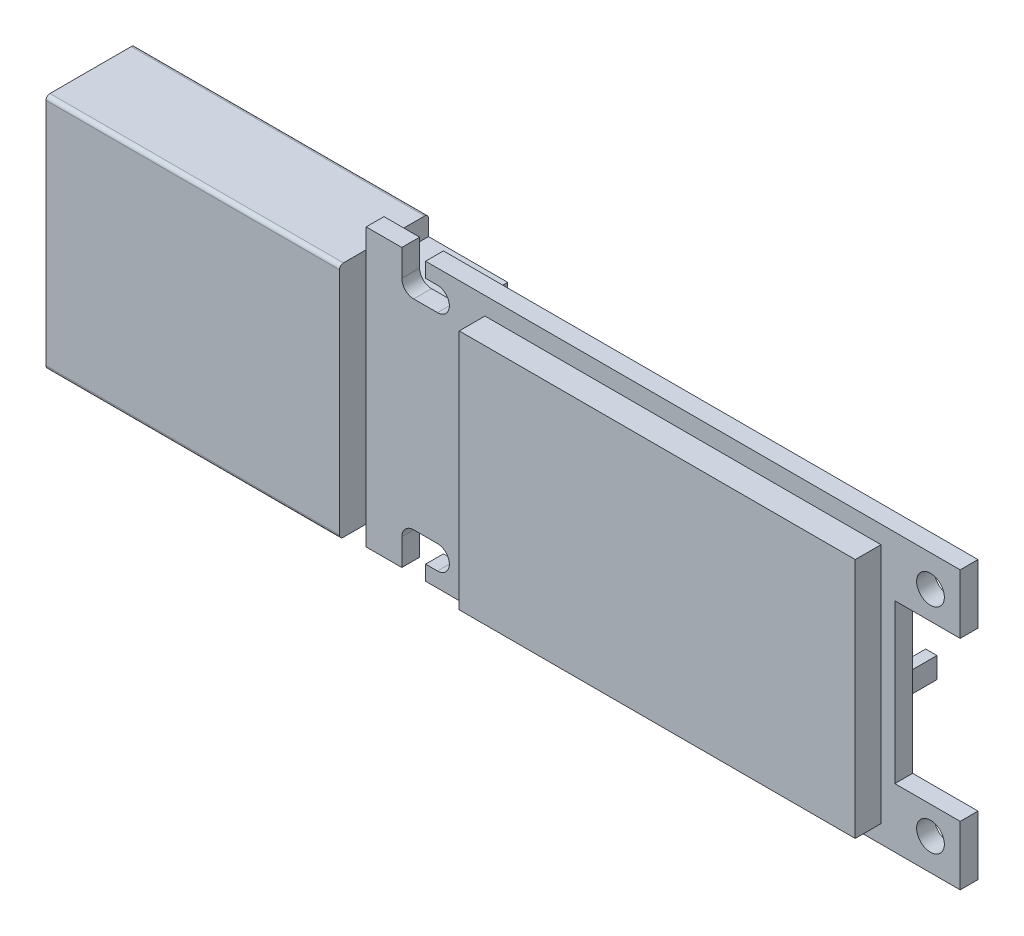
SolidWorks part; units mm, degrees
ref_plane "Plan de face" through (0, 0, 0) normal (0, 0, 1) x (1, 0, 0)
ref_plane "Plan de dessus" through (0, 0, 0) normal (0, 1, 0) x (1, 0, 0)
ref_plane "Plan de droite" through (0, 0, 0) normal (1, 0, 0) x (0, 0, -1)
sketch "Esquisse1" plane through (0, 0, 0) normal (0, 0, 1) x (1, 0, 0)
  line L1 (-7.41, 6) -> (7.41, 6)
  line L2 (-7.41, 6) -> (-7.41, -6)
  line L3 (-7.41, -6) -> (7.41, -6)
  line L4 (7.41, 6) -> (7.41, -6)
  line L5 (-7.41, 6) -> (7.41, -6) construction
  line L6 (-7.41, -6) -> (7.41, 6) construction
  point P0 (0, 0)
  dimension "D1" = 14.82
  dimension "D2" = 12
extrude "Boss.-Extru.1" add sketch "Esquisse1" along normal blind 4.5
sketch "Esquisse2" plane through (-7.41, 0, 0) normal (-1, 0, 0) x (0, 0, 1)
  line L0 (4.5, 6) -> (0, 6) construction
  line L1 (0.3, 5.7) -> (2.3, 5.7)
  line L2 (0.3, 5.7) -> (0.3, -5.7)
  line L3 (0.3, -5.7) -> (2.3, -5.7)
  line L4 (2.3, 5.7) -> (2.3, -5.7)
  line L5 (0, 6) -> (0, -6) construction
  line L6 (4.5, -6) -> (0, -6) construction
  dimension "D1" = 2
  dimension "D2" = 0.3
  dimension "D3" = 0.3
  dimension "D4" = 0.3
extrude "Enlèv. mat.-Extru.1" cut sketch "Esquisse2" against normal blind 9
fillet "Congé1" radius 0.2 4 edges at (0, -6, 0) (0, -6, 4.5) (0, 6, 0) (0, 6, 4.5)
ref_plane "Plan1" through (0, 0, 2.25) normal (0, 0, 1) x (1, 0, 0)
sketch "Esquisse3" plane through (0, 0, 2.25) normal (0, 0, 1) x (1, 0, 0)
  line L0 (0, 0) -> (36.7919, 0) construction
  line L1 (7.41, 7) -> (37.41, 7)
  line L2 (7.41, 7) -> (7.41, -7)
  line L3 (7.41, -7) -> (37.41, -7)
  line L4 (37.41, 7) -> (37.41, -7)
  line L5 (7.41, -5.8) -> (7.41, 5.8) construction
  point P7 (37.41, 0)
  dimension "D1" = 14
  dimension "D2" = 30
extrude "Boss.-Extru.2" add sketch "Esquisse3" along normal blind 0.9
sketch "Esquisse4" plane through (0, 0, 0) normal (0, 0, -1) x (-1, 0, 0)
  line L0 (7.41, 0) -> (-7.41, 0) construction
  line L1 (7.41, 5.8) -> (7.41, -5.8) construction
  line L2 (-7.41, 6) -> (-7.41, -6) construction
  line L3 (-7.41, 6) -> (7.41, 6) construction
  line L4 (0.41, 4.2) -> (2.41, 4.2)
  line L5 (0.41, 4.2) -> (0.41, 1.7)
  line L6 (0.41, 1.7) -> (2.41, 1.7)
  line L7 (2.41, 4.2) -> (2.41, 1.7)
  line L8 (2.41, -4.2) -> (2.41, -1.7)
  line L9 (0.41, -1.7) -> (2.41, -1.7)
  line L10 (0.41, -4.2) -> (0.41, -1.7)
  line L11 (0.41, -4.2) -> (2.41, -4.2)
  dimension "D1" = 2
  dimension "D2" = 2.5
  dimension "D3" = 1.8
  dimension "D4" = 5
extrude "Enlèv. mat.-Extru.2" cut sketch "Esquisse4" against normal up to next
sketch "Esquisse5" plane through (0, 0, 3.15) normal (0, 0, 1) x (1, 0, 0)
  line L0 (37.41, 0) -> (7.41, 0) construction
  line L1 (37.41, -7) -> (37.41, 7) construction
  line L2 (7.41, 6) -> (7.41, -6) construction
  line L3 (35.91, 7) -> (35.91, -7) construction
  line L4 (37.41, 4) -> (34.11, 4)
  line L5 (37.41, 4) -> (37.41, -4)
  line L6 (37.41, -4) -> (34.11, -4)
  line L7 (34.11, 4) -> (34.11, -4)
  line L8 (37.41, 7) -> (7.41, 7) construction
  line L9 (7.41, -7) -> (37.41, -7) construction
  line L10 (7.41, 7) -> (7.41, 6) construction
  line L11 (9.81, 5.65) -> (11.01, 5.65) construction
  line L12 (9.81, 6.25) -> (11.01, 6.25)
  line L13 (9.81, 5.05) -> (11.01, 5.05)
  line L14 (7.41, -5.8) -> (7.41, 5.8) construction
  line L15 (9.81, -5.65) -> (11.01, -5.65) construction
  line L16 (9.81, -6.25) -> (11.01, -6.25)
  line L17 (9.81, -5.05) -> (11.01, -5.05)
  circle A0 centre (35.91, 5.4) radius 0.7
  circle A1 centre (35.91, -5.4) radius 0.7
  arc A2 (9.81, 6.25) -> (9.81, 5.05) centre (9.81, 5.65) ccw
  arc A3 (11.01, 5.05) -> (11.01, 6.25) centre (11.01, 5.65) ccw
  arc A4 (9.81, -6.25) -> (9.81, -5.05) centre (9.81, -5.65) cw
  arc A5 (11.01, -5.05) -> (11.01, -6.25) centre (11.01, -5.65) cw
  point P10 (34.11, 0)
  point P25 (10.41, 5.65)
  point P34 (10.41, -5.65)
  dimension "D4" = 1.4
  dimension "D1" = 8
  dimension "D2" = 3.3
  dimension "D3" = 28.5
  dimension "D5" = 10.8
  dimension "D6" = 3
  dimension "D7" = 1.2
  dimension "D8" = 1.2
  dimension "D9" = 11.3
extrude "Enlèv. mat.-Extru.3" cut sketch "Esquisse5" against normal through all
sketch "Esquisse6" plane through (0, 0, 3.15) normal (0, 0, 1) x (1, 0, 0)
  line L0 (-7.41, 0) -> (34.11, 0) construction
  line L1 (13.41, 6.1) -> (33.41, 6.1)
  line L2 (13.41, 6.1) -> (13.41, -6.1)
  line L3 (13.41, -6.1) -> (33.41, -6.1)
  line L4 (33.41, 6.1) -> (33.41, -6.1)
  line L5 (-7.41, 5.8) -> (-7.41, -5.8) construction
  line L6 (34.11, 4) -> (34.11, -4) construction
  line L7 (7.41, 6) -> (7.41, -6) construction
  point P10 (13.41, 0)
  dimension "D1" = 12.2
  dimension "D2" = 20
  dimension "D3" = 26
extrude "Boss.-Extru.3" add sketch "Esquisse6" along normal blind 1.3
sketch "Esquisse7" plane through (0, 0, 2.25) normal (0, 0, -1) x (-1, 0, 0)
  line L1 (-30.8694, 3.363) -> (-22.672, 3.363)
  line L2 (-30.8694, 3.363) -> (-30.8694, -3.4681)
  line L3 (-30.8694, -3.4681) -> (-22.672, -3.4681)
  line L4 (-22.672, 3.363) -> (-22.672, -3.4681)
  line L5 (-18.4681, -2.207) -> (-17.1019, -2.207)
  line L6 (-18.4681, -2.207) -> (-18.4681, -4.3089)
  line L7 (-18.4681, -4.3089) -> (-17.1019, -4.3089)
  line L8 (-17.1019, -2.207) -> (-17.1019, -4.3089)
  line L9 (-15.3153, -2.207) -> (-14.0541, -2.207)
  line L10 (-15.3153, -2.207) -> (-15.3153, -4.3089)
  line L11 (-15.3153, -4.3089) -> (-14.0541, -4.3089)
  line L12 (-14.0541, -2.207) -> (-14.0541, -4.3089)
  line L13 (-19.6242, 3.363) -> (-17.1019, 3.363)
  line L14 (-19.6242, 3.363) -> (-19.6242, 2.3121)
  line L15 (-19.6242, 2.3121) -> (-17.1019, 2.3121)
  line L16 (-17.1019, 3.363) -> (-17.1019, 2.3121)
  line L17 (-33.9366, 0.3664) -> (-33.3662, 0.3664)
  line L18 (-33.9366, 0.3664) -> (-33.9366, -0.6888)
  line L19 (-33.9366, -0.6888) -> (-33.3662, -0.6888)
  line L20 (-33.3662, 0.3664) -> (-33.3662, -0.6888)
extrude "Boss.-Extru.4" add sketch "Esquisse7" along normal blind 1.4
sketch "Esquisse8" plane through (0, 0, 2.25) normal (0, 0, -1) x (-1, 0, 0)
  line L0 (-7.41, 6) -> (-7.41, -6) construction
  line L1 (-7.41, 5) -> (-11.41, 5)
  line L2 (-7.41, 5) -> (-7.41, -5)
  line L3 (-7.41, -5) -> (-11.41, -5)
  line L4 (-11.41, 5) -> (-11.41, -5)
  line L5 (7.41, 0) -> (-34.11, 0) construction
  line L6 (7.41, 5.8) -> (7.41, -5.8) construction
  line L7 (-34.11, 4) -> (-34.11, -4) construction
  point P12 (-11.41, 0)
  dimension "D1" = 10
  dimension "D2" = 4
extrude "Boss.-Extru.5" add sketch "Esquisse8" along normal up to surface (2.25 mm away) up to face at (-1.41, -2.95, 0)
sketch "Esquisse9" plane through (0, 0, 3.15) normal (0, 0, 1) x (1, 0, 0)
  line L0 (37.41, 7) -> (7.41, 7) construction
  line L1 (9.21, 7) -> (10.41, 7)
  line L2 (9.21, 7) -> (9.21, 5.65)
  line L3 (9.21, 5.65) -> (10.41, 5.65)
  line L4 (10.41, 7) -> (10.41, 5.65)
  line L5 (9.21, 5.65) -> (11.61, 5.65) construction
  line L6 (7.41, 0) -> (13.41, 0) construction
  line L7 (7.41, -5.8) -> (7.41, 5.8) construction
  line L8 (13.41, 6.1) -> (13.41, -6.1) construction
  line L9 (9.21, -5.65) -> (11.61, -5.65) construction
  line L10 (10.41, -7) -> (10.41, -5.65)
  line L11 (9.21, -5.65) -> (10.41, -5.65)
  line L12 (9.21, -7) -> (9.21, -5.65)
  line L13 (9.21, -7) -> (10.41, -7)
  arc A0 (9.81, 6.25) -> (9.81, 5.05) centre (9.81, 5.65) ccw construction
  arc A1 (11.01, 5.05) -> (11.01, 6.25) centre (11.01, 5.65) ccw construction
extrude "Enlèv. mat.-Extru.4" cut sketch "Esquisse9" against normal through all
